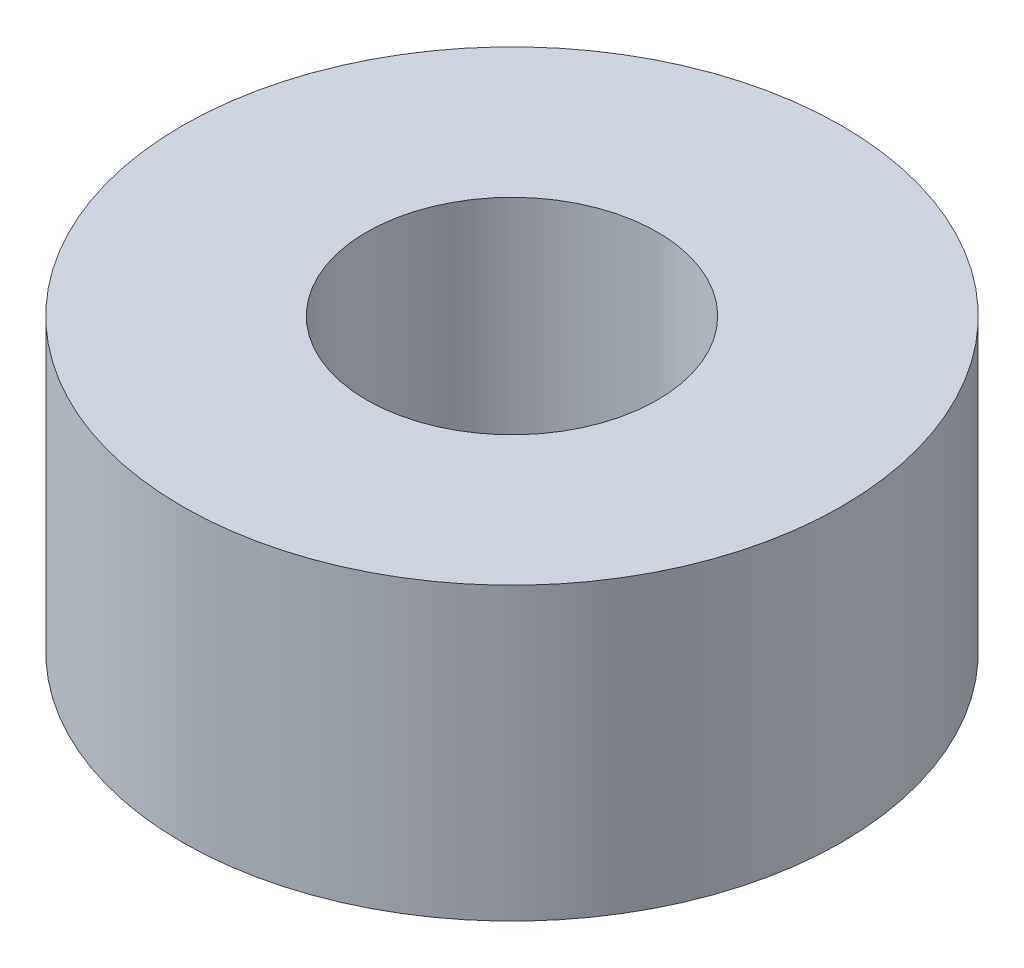
SolidWorks part; units mm, degrees
material "ABS PC"
ref_plane "Front Plane" through (0, 0, 0) normal (0, 0, 1) x (1, 0, 0)
ref_plane "Top Plane" through (0, 0, 0) normal (0, 1, 0) x (1, 0, 0)
ref_plane "Right Plane" through (0, 0, 0) normal (1, 0, 0) x (0, 0, -1)
sketch "Sketch1" plane through (0, 0, 0) normal (0, 1, 0) x (1, 0, 0)
  circle A0 centre (0, 0) radius 3.4
  circle A1 centre (0, 0) radius 1.5
  dimension "D1" = 3
  dimension "D2" = 6.8
extrude "Spacer Height" add sketch "Sketch1" along normal blind 3
